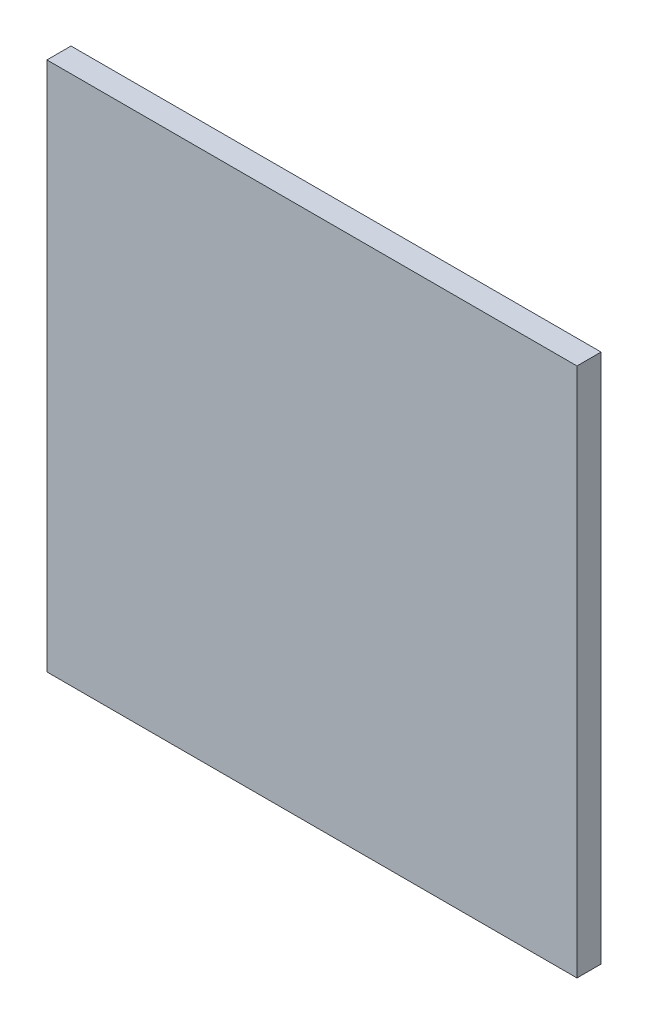
SolidWorks part; units mm, degrees
ref_plane "Front Plane" through (0, 0, 0) normal (0, 0, 1) x (1, 0, 0)
ref_plane "Top Plane" through (0, 0, 0) normal (0, 1, 0) x (1, 0, 0)
ref_plane "Right Plane" through (0, 0, 0) normal (1, 0, 0) x (0, 0, -1)
sketch "Sketch1" plane through (0, 0, 0) normal (0, 0, 1) x (1, 0, 0)
  line L1 (0, 0) -> (279.4, 0)
  line L2 (0, 0) -> (0, 279.4)
  line L3 (0, 279.4) -> (279.4, 279.4)
  line L4 (279.4, 0) -> (279.4, 279.4)
  dimension "D1" = 279.4
  dimension "D2" = 279.4
extrude "Boss-Extrude1" add sketch "Sketch1" along normal blind 12.7
